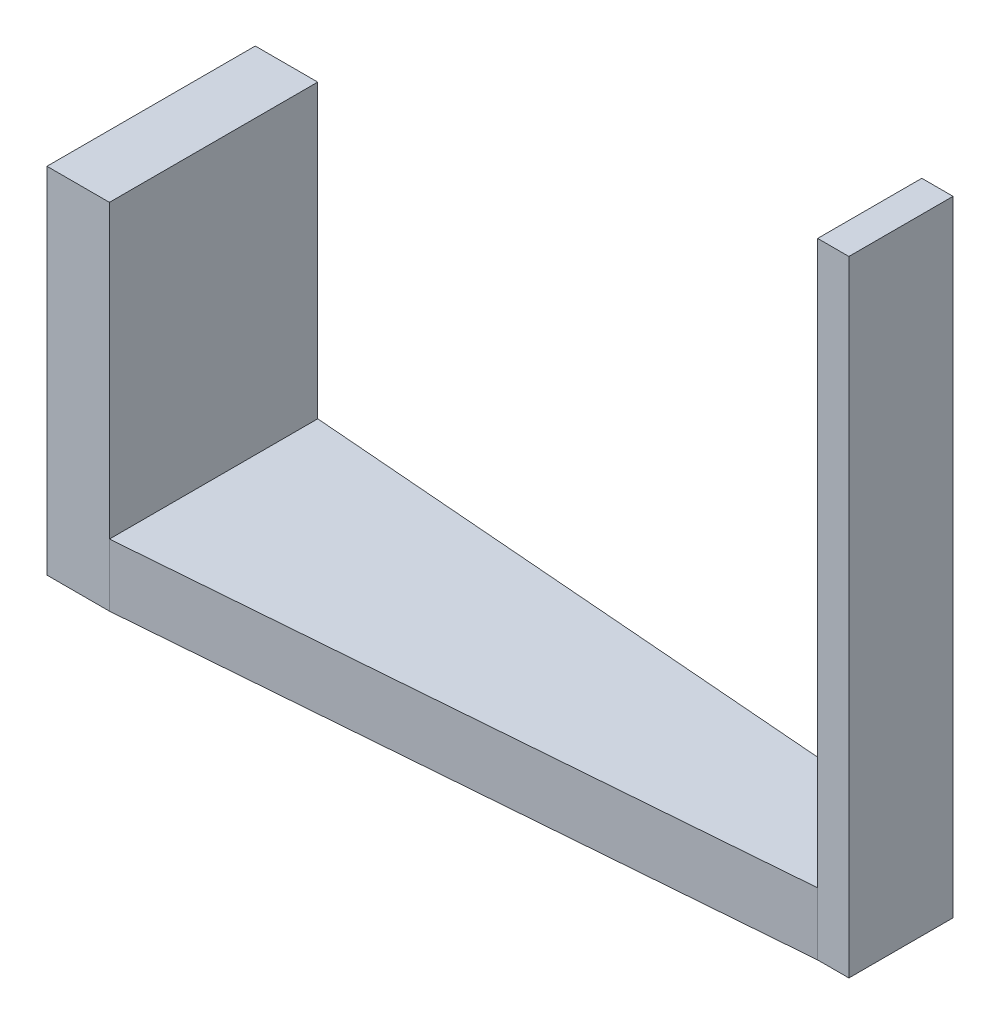
SolidWorks part; units mm, degrees
ref_plane "Front Plane" through (0, 0, 0) normal (0, 0, 1) x (1, 0, 0)
ref_plane "Top Plane" through (0, 0, 0) normal (0, 1, 0) x (1, 0, 0)
ref_plane "Right Plane" through (0, 0, 0) normal (1, 0, 0) x (0, 0, -1)
sketch "Sketch1" plane through (0, 0, 0) normal (0, 1, 0) x (1, 0, 0)
  line L0 (18, 2.5) -> (16.5, 2.5)
  line L1 (-18, -5) -> (-15, -5)
  line L2 (-18, -5) -> (-18, 5)
  line L3 (-18, 5) -> (-15, 5)
  line L4 (18, -2.5) -> (18, 2.5)
  line L5 (-18, -5) -> (10.6667, 2.963) construction
  line L6 (-18, 5) -> (10.6667, -2.963) construction
  line L7 (16.5, 2.5) -> (-15, 5)
  line L8 (18, -2.5) -> (16.5, -2.5)
  line L9 (16.5, -2.5) -> (-15, -5)
  point P0 (0, 0)
  point P1 (17.25, 2.5)
  dimension "D1" = 10
  dimension "D2" = 2.5
  dimension "D3" = 1.5
  dimension "D4" = 1.5
  dimension "D5" = 3
  dimension "D6" = 3
  dimension "D7" = 2.5
extrude "Boss-Extrude1" add sketch "Sketch1" along normal blind 3
sketch "Sketch2" plane through (0, 3, 0) normal (0, 1, 0) x (1, 0, 0)
  line L1 (-18, 5) -> (-15, 5)
  line L2 (-18, 5) -> (-18, -5)
  line L3 (-18, -5) -> (-15, -5)
  line L4 (-15, 5) -> (-15, -5)
extrude "Boss-Extrude2" add sketch "Sketch2" along normal blind 14
sketch "Sketch3" plane through (0, 3, 0) normal (0, 1, 0) x (1, 0, 0)
  line L1 (18, -2.5) -> (16.5, -2.5)
  line L2 (18, -2.5) -> (18, 2.5)
  line L3 (18, 2.5) -> (16.5, 2.5)
  line L4 (16.5, -2.5) -> (16.5, 2.5)
extrude "Boss-Extrude3" add sketch "Sketch3" along normal blind 27
